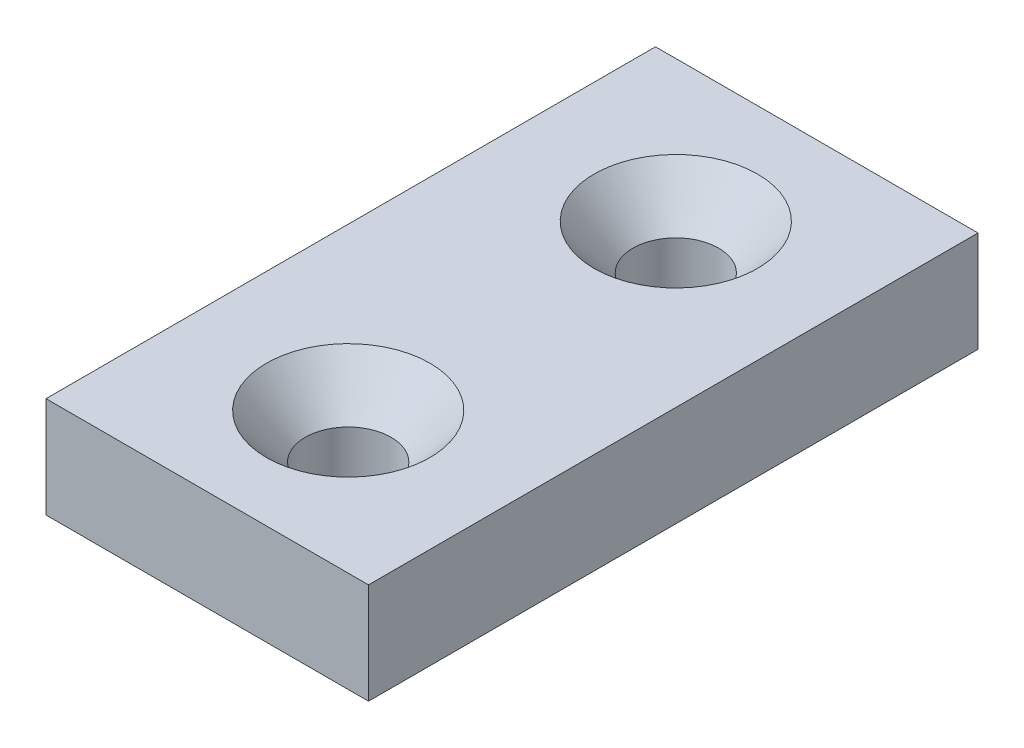
SolidWorks part; units mm, degrees
ref_plane "Front Plane" through (0, 0, 0) normal (0, 0, 1) x (1, 0, 0)
ref_plane "Top Plane" through (0, 0, 0) normal (0, 1, 0) x (1, 0, 0)
ref_plane "Right Plane" through (0, 0, 0) normal (1, 0, 0) x (0, 0, -1)
sketch "Sketch1" plane through (0, 0, 0) normal (0, 0, 1) x (1, 0, 0)
  line L0 (0, 3.9688) -> (0, -3.9688)
  line L1 (-12.7, 0) -> (12.7, 0) construction
  point P6 (0, 0)
  dimension "Width" = 25.4
  dimension "Thk" = 7.9375
sketch "Sketch2" plane through (0, 0, 0) normal (1, 0, 0) x (0, 0, -1)
  line L0 (152.4, 0) -> (-152.4, 0)
  point P4 (0, 0)
  dimension "Length" = 304.8
sketch "Sketch3" plane through (0, 0, 0) normal (0, 0, 1) x (1, 0, 0)
  line L1 (12.7, 3.9688) -> (-12.7, 3.9688)
  line L2 (12.7, 3.9688) -> (12.7, -3.9688)
  line L3 (12.7, -3.9688) -> (-12.7, -3.9688)
  line L4 (-12.7, 3.9688) -> (-12.7, -3.9688)
  line L5 (12.7, 3.9688) -> (-12.7, -3.9688) construction
  line L6 (12.7, -3.9688) -> (-12.7, 3.9688) construction
  point P0 (0, 0)
extrude "Boss-Extrude1" add sketch "Sketch3" along normal mid plane 48
sketch "Sketch5" plane through (0, 3.9688, 0) normal (0, 1, 0) x (1, 0, 0)
  line L0 (12.7, 24) -> (-12.7, 24) construction
  line L1 (12.7, 24) -> (12.7, -24) construction
  line L2 (12.7, 0) -> (-12.7, 0) construction
  circle A0 centre (0, 12.9) radius 3.5
  circle A4 centre (0, -12.9) radius 3.5
  dimension "D1" = 7
  dimension "D2" = 11.1
  dimension "D3" = 12.7
hole_wizard "CSK for 1/4 Flat Head Machine Screw1" positions "Sketch6" profile "Sketch7" countersink size "1/4" standard "ANSI Inch" end condition through all
sketch "Sketch6" plane through (0, 3.9688, 0) normal (0, 1, 0) x (-1, 0, 0)
  point P0 (0, 12.9)
  point P3 (0, -12.9)
sketch "Sketch7" plane through (0, 3.9688, 12.9) normal (1, 0, 0) x (0, 0, 1)
  line L0 (0, 0) -> (0, 7.9375)
  line L1 (0, 7.9375) -> (3.3782, 7.9375)
  line L2 (3.3782, 7.9375) -> (3.3782, 3.5209)
  line L3 (3.3782, 3.5209) -> (6.4389, 0)
  line L5 (6.4389, 0) -> (0, 0)
  line L6 (-3.3782, 3.5209) -> (-6.4389, 0) construction
  line L11 (0, -6.35) -> (0, 107.95) construction
  dimension "Thru Hole Dia." = 6.7564
  dimension "Thru Hole Depth" = 7.9375
  dimension "Near C'Sink Dia." = 12.8778
  dimension "Near C'Sink Angle" = 82
